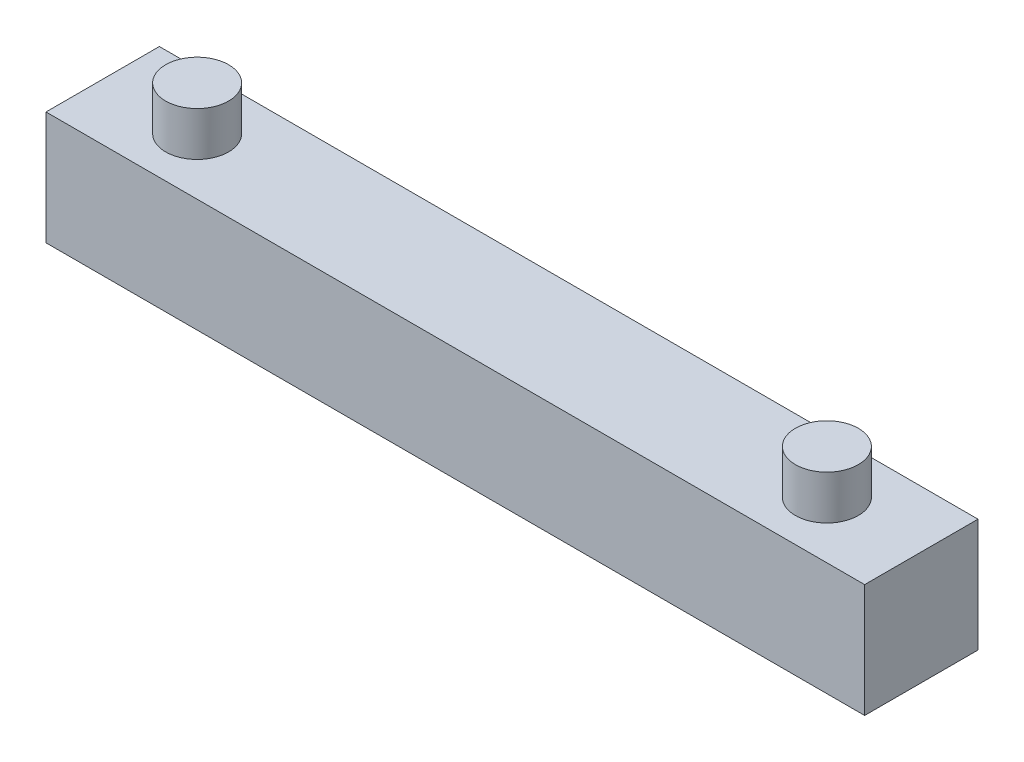
SolidWorks part; units mm, degrees
ref_plane "Front Plane" through (0, 0, 0) normal (0, 0, 1) x (1, 0, 0)
ref_plane "Top Plane" through (0, 0, 0) normal (0, 1, 0) x (1, 0, 0)
ref_plane "Right Plane" through (0, 0, 0) normal (1, 0, 0) x (0, 0, -1)
sketch "Sketch1" plane through (0, 0, 0) normal (0, 0, 1) x (1, 0, 0)
  line L1 (0, 0) -> (65, 0)
  line L2 (0, 0) -> (0, 9)
  line L3 (0, 9) -> (65, 9)
  line L4 (65, 0) -> (65, 9)
  dimension "D1" = 65
  dimension "D2" = 9
extrude "Boss-Extrude1" add sketch "Sketch1" along normal blind 9
sketch "Sketch2" plane through (0, 9, 0) normal (0, 1, 0) x (1, 0, 0)
  circle A0 centre (7.5, -4.5) radius 2.5
  circle A1 centre (57.5, -4.5) radius 2.5
  dimension "D2" = 5
  dimension "D1" = 50
extrude "Boss-Extrude3" add sketch "Sketch2" along normal blind 3.5
